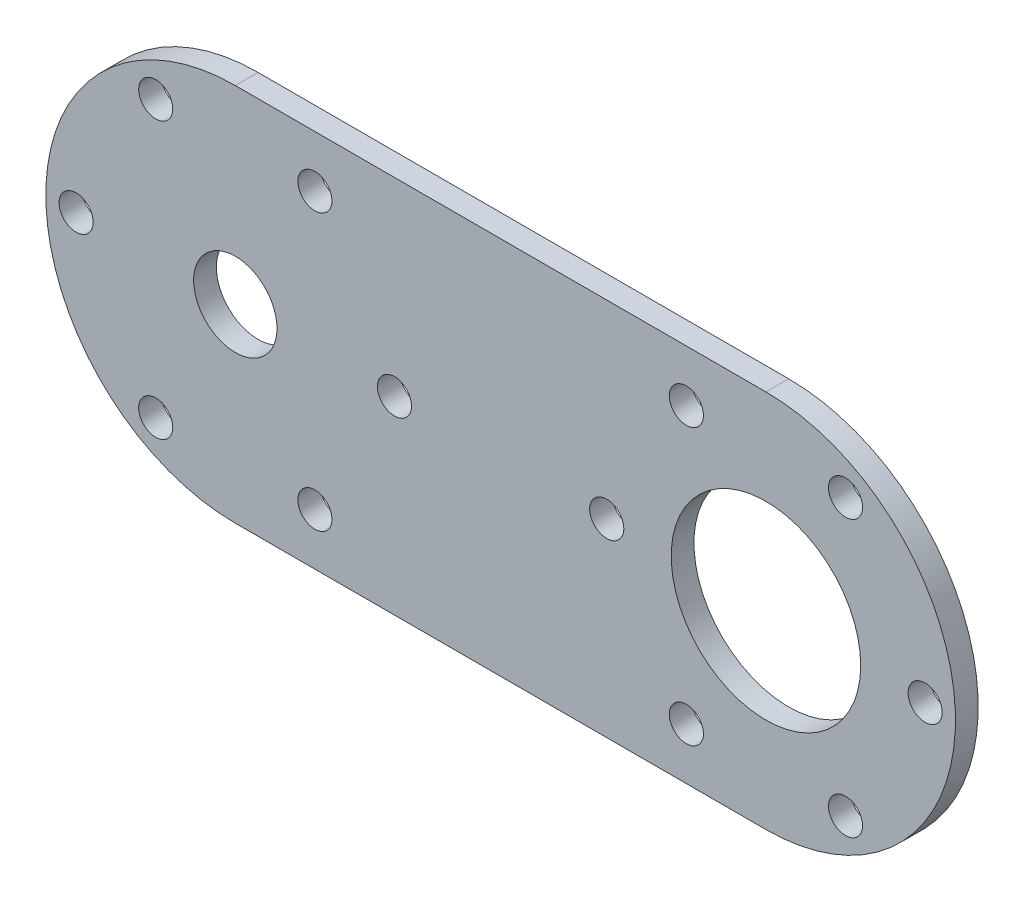
SolidWorks part; units mm, degrees
ref_plane "Alzado" through (0, 0, 0) normal (0, 0, 1) x (1, 0, 0)
ref_plane "Planta" through (0, 0, 0) normal (0, 1, 0) x (1, 0, 0)
ref_plane "Vista lateral" through (0, 0, 0) normal (1, 0, 0) x (0, 0, -1)
sketch "Croquis1" plane through (0, 0, 0) normal (0, 0, 1) x (1, 0, 0)
  line L0 (0, 0) -> (70, 0) construction
  line L1 (0, 25) -> (70, 25)
  line L2 (70, -25) -> (0, -25)
  circle A0 centre (0, 0) radius 25
  circle A1 centre (70, 0) radius 25
  circle A2 centre (70, 0) radius 12.5
  dimension "D1" = 50
  dimension "D2" = 50
  dimension "D4" = 25
  dimension "D3" = 70
extrude "Saliente-Extruir1" add sketch "Croquis1" along normal blind 3
hole_wizard "Taladro de margen para M42" positions "Croquis4" profile "Croquis5" hole size "M4" standard "ISO" end condition through all
sketch "Croquis4" plane through (0, 0, 3) normal (0, 0, 1) x (1, 0, 0)
  circle A0 centre (70, 0) radius 12.5 construction
  point P0 (-21, 0)
  point P2 (91, 0)
  point P14 (-10.5, 18.1865)
  point P15 (10.5, 18.1865)
  point P16 (21, 0)
  point P17 (10.5, -18.1865)
  point P18 (-10.5, -18.1865)
  point P26 (80.5, -18.1865)
  point P27 (59.5, -18.1865)
  point P28 (49, 0)
  point P29 (59.5, 18.1865)
  point P30 (80.5, 18.1865)
  dimension "D1" = 21
  dimension "D2" = 21
  dimension "D3" = 6
  dimension "D4" = 6
sketch "Croquis5" plane through (-21, 0, 3) normal (1, 0, 0) x (0, -1, 0)
  line L0 (0, 0) -> (0, 3)
  line L1 (0, 3) -> (2.25, 3)
  line L2 (2.25, 3) -> (2.25, 0)
  line L5 (2.25, 0) -> (0, 0)
  line L11 (0, -6.35) -> (0, 107.95) construction
  dimension "Diámetro de taladro hasta el siguiente" = 4.5
  dimension "Profundidad de taladro hasta el siguiente" = 3
hole_wizard "Taladro de margen para M101" positions "Croquis6" profile "Croquis7" hole size "M10" standard "ISO" end condition through all
sketch "Croquis6" plane through (0, 0, 3) normal (0, 0, 1) x (1, 0, 0)
  point P0 (0, 0)
sketch "Croquis7" plane through (0, 0, 3) normal (1, 0, 0) x (0, -1, 0)
  line L0 (0, 0) -> (0, 3)
  line L1 (0, 3) -> (5.5, 3)
  line L2 (5.5, 3) -> (5.5, 0)
  line L5 (5.5, 0) -> (0, 0)
  line L11 (0, -6.35) -> (0, 107.95) construction
  dimension "Diámetro de taladro hasta el siguiente" = 11
  dimension "Profundidad de taladro hasta el siguiente" = 3
